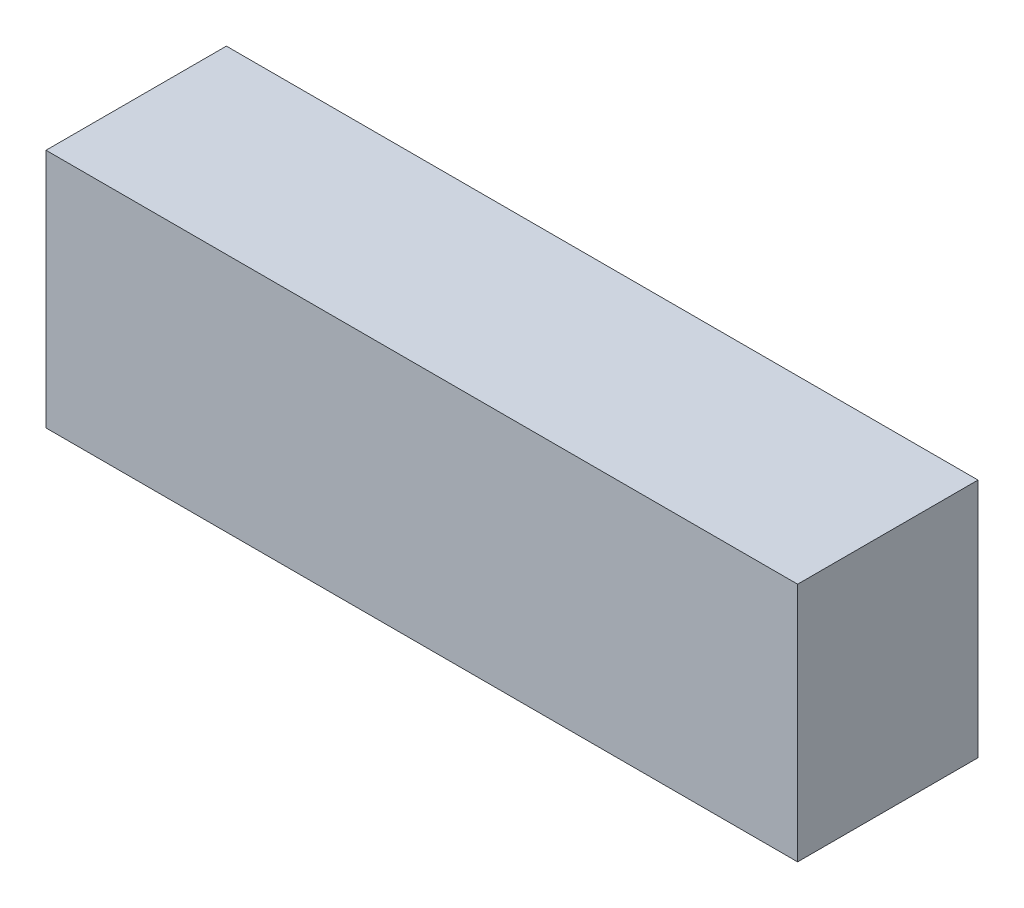
SolidWorks part; units mm, degrees
ref_plane "Front Plane" through (0, 0, 0) normal (0, 0, 1) x (1, 0, 0)
ref_plane "Top Plane" through (0, 0, 0) normal (0, 1, 0) x (1, 0, 0)
ref_plane "Right Plane" through (0, 0, 0) normal (1, 0, 0) x (0, 0, -1)
sketch "Sketch1" plane through (0, 0, 0) normal (0, 1, 0) x (1, 0, 0)
  line L1 (317.5, -76.2) -> (-317.5, -76.2)
  line L2 (317.5, -76.2) -> (317.5, 76.2)
  line L3 (317.5, 76.2) -> (-317.5, 76.2)
  line L4 (-317.5, -76.2) -> (-317.5, 76.2)
  line L5 (317.5, -76.2) -> (-317.5, 76.2) construction
  line L6 (317.5, 76.2) -> (-317.5, -76.2) construction
  point P0 (0, 0)
  dimension "D1" = 635
  dimension "D2" = 152.4
extrude "Boss-Extrude1" add sketch "Sketch1" along normal blind 203.2
